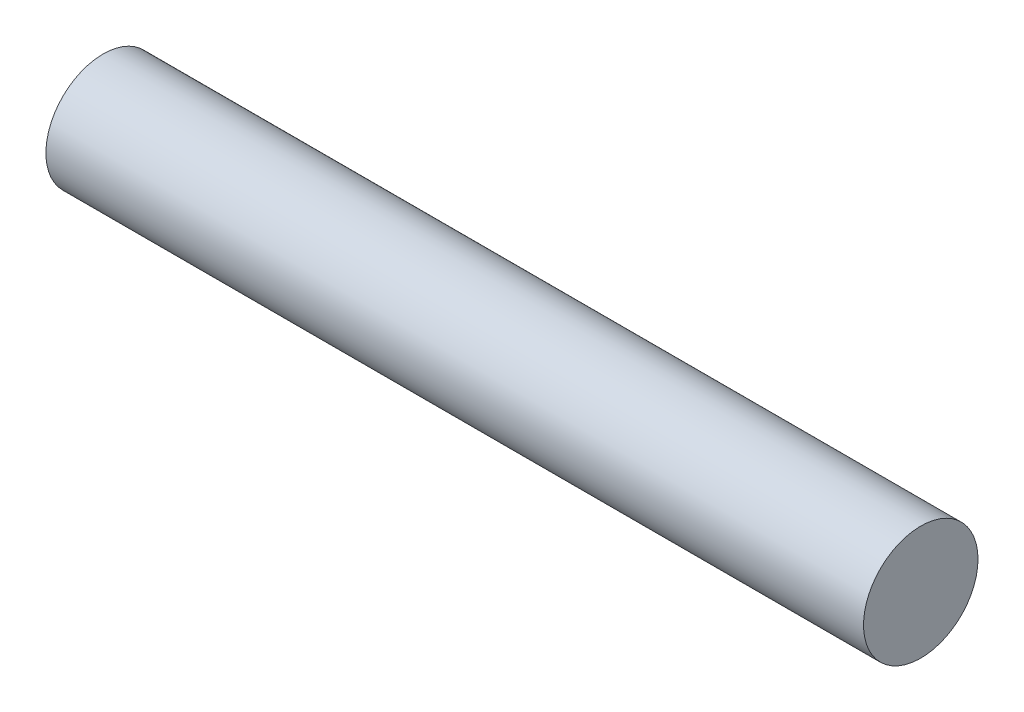
SolidWorks part; units mm, degrees
material "Plain Carbon Steel"
ref_plane "Front Plane" through (0, 0, 0) normal (0, 0, 1) x (1, 0, 0)
ref_plane "Top Plane" through (0, 0, 0) normal (0, 1, 0) x (1, 0, 0)
ref_plane "Right Plane" through (0, 0, 0) normal (1, 0, 0) x (0, 0, -1)
sketch "Sketch1" plane through (0, 0, 0) normal (1, 0, 0) x (0, 0, -1)
  circle A0 centre (0, 0) radius 11.1125
extrude "Boss-Extrude1" add sketch "Sketch1" along normal mid plane 158.75
